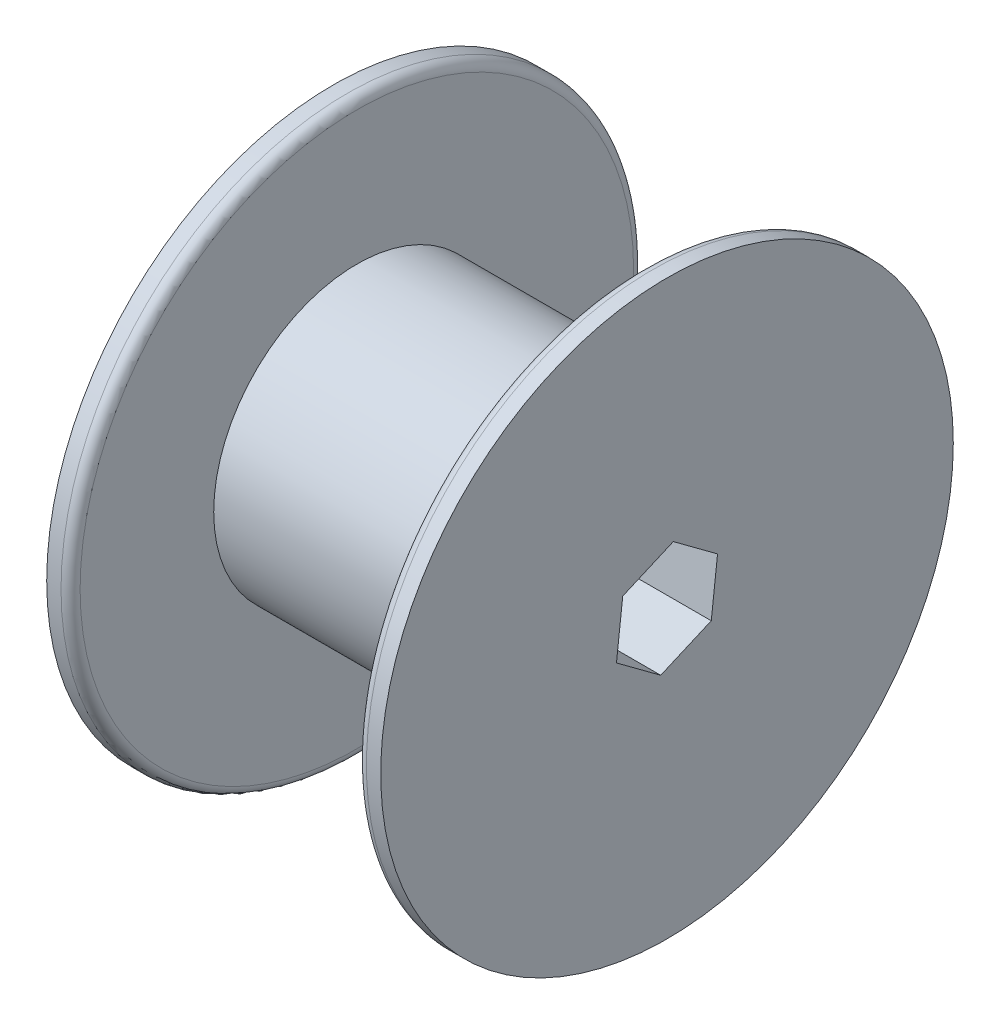
SolidWorks part; units mm, degrees
ref_plane "Front" through (0, 0, 0) normal (0, 0, 1) x (1, 0, 0)
ref_plane "Top" through (0, 0, 0) normal (0, 1, 0) x (1, 0, 0)
ref_plane "Right" through (0, 0, 0) normal (1, 0, 0) x (0, 0, -1)
sketch "Sketch1" plane through (0, 0, 0) normal (1, 0, 0) x (0, 0, -1)
  circle A0 centre (0, 0) radius 19.05
  dimension "D1" = 38.1
extrude "Boss-Extrude1" add sketch "Sketch1" along normal blind 38.1
sketch "Sketch2" plane through (0, 0, 0) normal (-1, 0, 0) x (0, 0, 1)
  circle A0 centre (0, 0) radius 38.1
  circle A1 centre (0, 0) radius 19.05 construction
  dimension "D1" = 19.05
extrude "Boss-Extrude2" add sketch "Sketch2" along normal blind 3.175
sketch "Sketch3" plane through (38.1, 0, 0) normal (1, 0, 0) x (0, 0, -1)
  circle A0 centre (0, 0) radius 38.1 construction
  circle A1 centre (0, 0) radius 38.1
extrude "Boss-Extrude3" add sketch "Sketch3" along normal blind 3.175
sketch "Sketch4" plane through (-3.175, 0, 0) normal (-1, 0, 0) x (0, 0, 1)
  circle A0 centre (0, 0) radius 6.35
  dimension "D1" = 12.7
extrude "Cut-Extrude1" cut sketch "Sketch4" against normal through all
fillet "Fillet1" radius 1.27 2 edges at (0, 0, 38.1) (38.1, 0, -38.1)
sketch "Sketch5" plane through (-3.175, 0, 0) normal (-1, 0, 0) x (0, 0, 1)
  line L1 (-5.8904, -4.3666) -> (0.8364, -7.2845)
  line L2 (0.8364, -7.2845) -> (6.7268, -2.9179)
  line L3 (6.7268, -2.9179) -> (5.8904, 4.3666)
  line L4 (5.8904, 4.3666) -> (-0.8364, 7.2845)
  line L5 (-0.8364, 7.2845) -> (-6.7268, 2.9179)
  line L6 (-6.7268, 2.9179) -> (-5.8904, -4.3666)
  circle A0 centre (0, 0) radius 6.35 construction
extrude "Cut-Extrude2" cut sketch "Sketch5" against normal through all
ref_plane "Mid_Plane" through (19.05, 0, 0) normal (-1, 0, 0) x (0, 0, 1)
